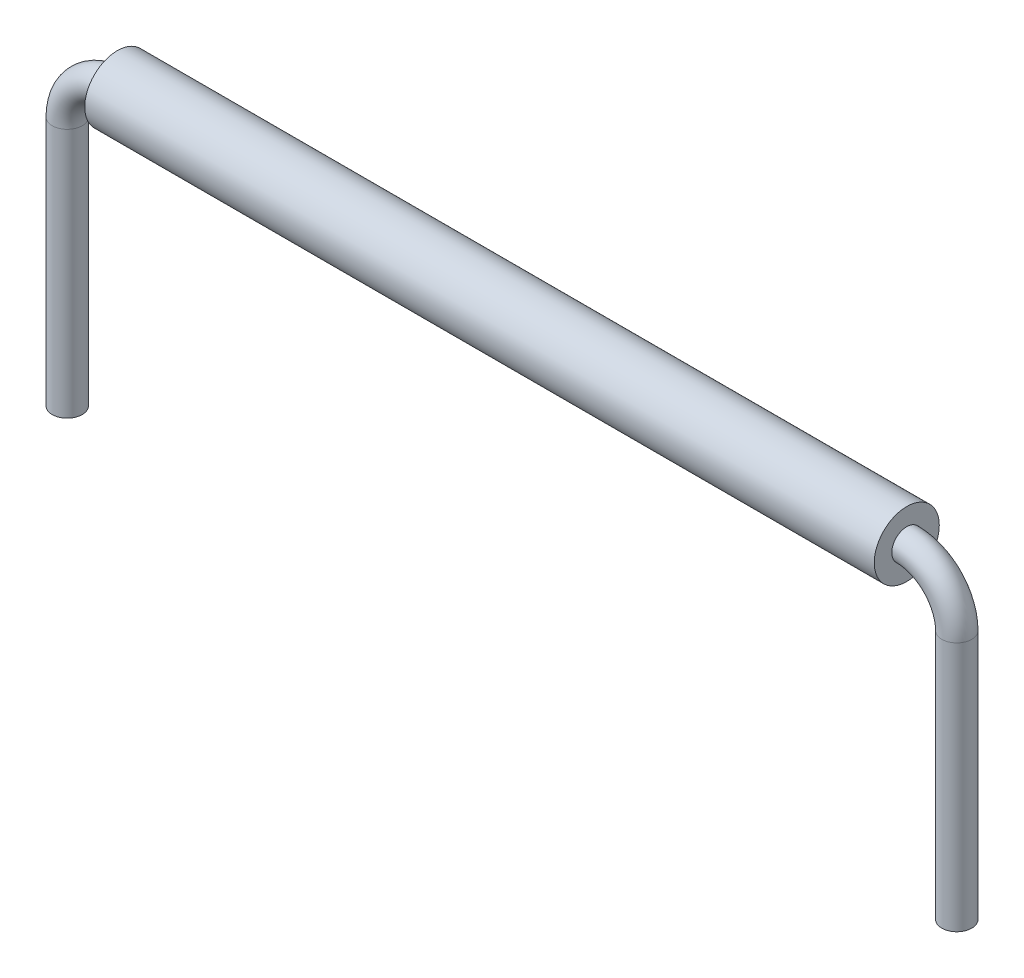
SolidWorks part; units mm, degrees
other "Wire"
other "Insulation"
ref_plane "Front Plane" through (0, 0, 0) normal (0, 0, 1) x (1, 0, 0)
ref_plane "Top Plane" through (0, 0, 0) normal (0, 1, 0) x (1, 0, 0)
ref_plane "Right Plane" through (0, 0, 0) normal (1, 0, 0) x (0, 0, -1)
sketch "Sketch1" plane through (0, 0, 0) normal (0, 0, 1) x (1, 0, 0)
  line L0 (-7.89, 0) -> (7.89, 0)
  line L1 (-8.89, -1) -> (-8.89, -6)
  line L2 (8.89, -1) -> (8.89, -6)
  line L3 (0, 0) -> (0, -6) construction
  line L4 (-8.89, -6) -> (8.89, -6) construction
  arc A0 (-7.89, 0) -> (-8.89, -1) centre (-7.89, -1) ccw
  arc A1 (7.89, 0) -> (8.89, -1) centre (7.89, -1) cw
  dimension "D1" = 1
  dimension "D2" = 17.78
  dimension "D3" = 6
sketch "Sketch2" plane through (0, 0, 0) normal (1, 0, 0) x (0, 0, -1)
  circle A0 centre (0, 0) radius 0.3
  dimension "D1" = 0.6
sweep "Sweep1" add profiles "Sketch2" path "Sketch1"
sketch "Sketch3" plane through (0, 0, 0) normal (1, 0, 0) x (0, 0, -1)
  circle A0 centre (0, 0) radius 0.65
  circle A1 centre (0, 0) radius 0.3
  dimension "D1" = 1.3
  dimension "D2" = 0.6
extrude "Boss-Extrude1" add sketch "Sketch3" along normal up to vertex (7.89 mm away) and the other way up to vertex (7.89 mm away) separate body up to point (7.89, 0, 0) other way up to point (-7.89, 0, 0)
